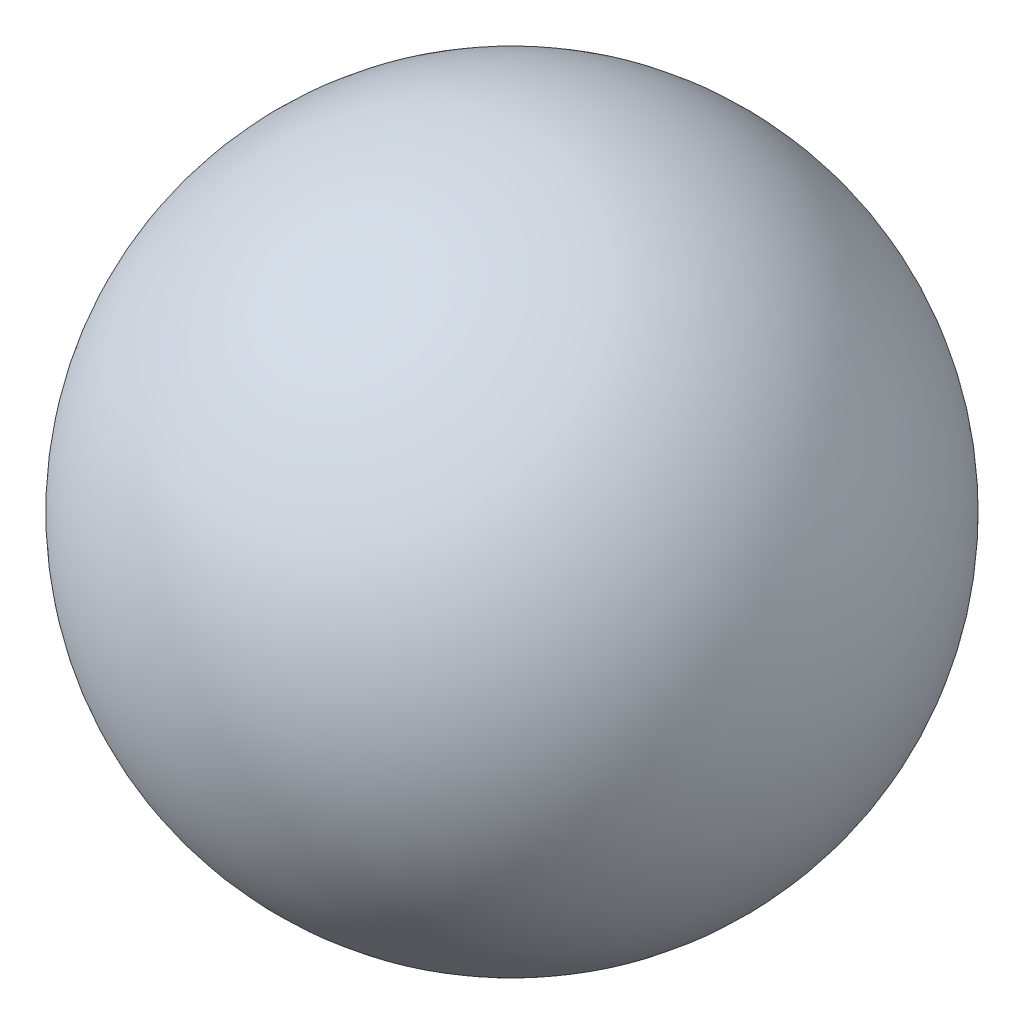
SolidWorks part; units mm, degrees
ref_plane "Przednia" through (0, 0, 0) normal (0, 0, 1) x (1, 0, 0)
ref_plane "Górna" through (0, 0, 0) normal (0, 1, 0) x (1, 0, 0)
ref_plane "Prawa" through (0, 0, 0) normal (1, 0, 0) x (0, 0, -1)
sketch "Szkic1" plane through (0, 0, 0) normal (0, 0, 1) x (1, 0, 0)
  line L0 (0, 0) -> (0, 8) construction
  line L1 (0, 8) -> (0, 0)
  arc A0 (0, 0) -> (0, 8) centre (0, 4) ccw
  dimension "D1" = 8
revolve "Obrót2" add sketch "Szkic1" angle 360 about L0
ref_plane "Płaszczyzna1" through (0, 8, 0) normal (0, 1, 0) x (1, 0, 0)
ref_plane "Płaszczyzna2" through (0, 0, 0) normal (0, -1, 0) x (-1, 0, 0)
